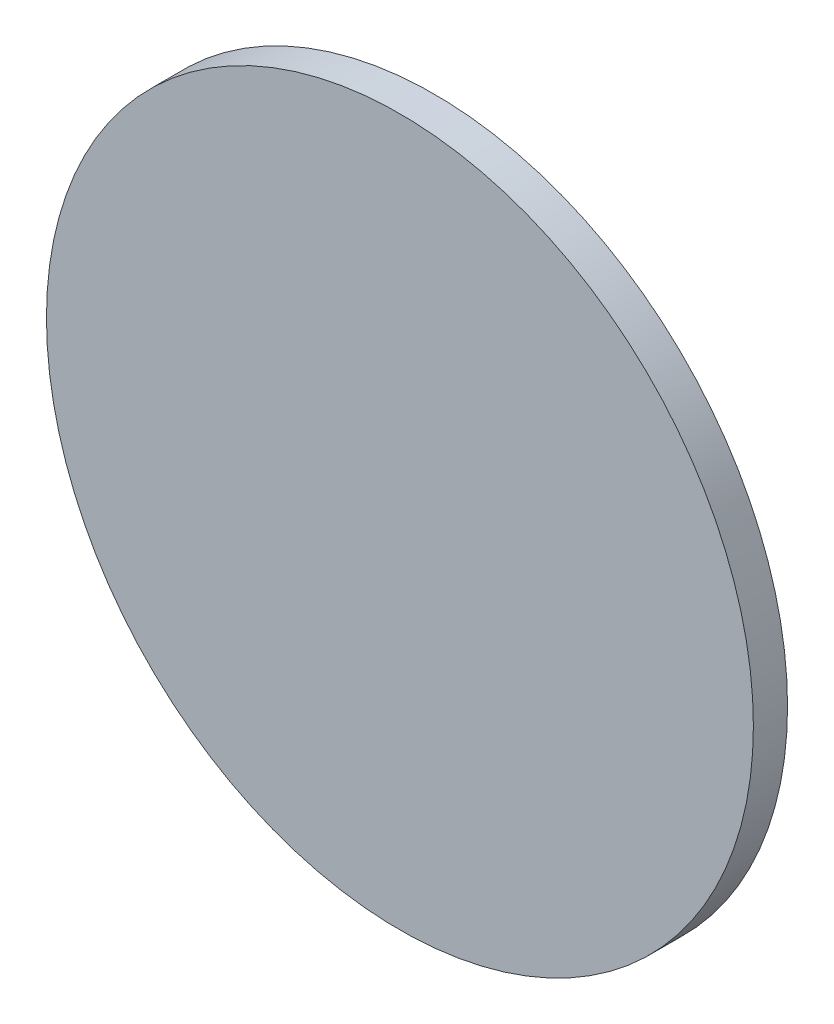
SolidWorks part; units mm, degrees
material "Bismuth"
ref_plane "Front" through (0, 0, 0) normal (0, 0, 1) x (1, 0, 0)
ref_plane "Top" through (0, 0, 0) normal (0, 1, 0) x (1, 0, 0)
ref_plane "Right" through (0, 0, 0) normal (1, 0, 0) x (0, 0, -1)
sketch "Sketch1" plane through (0, 0, 0) normal (0, 0, 1) x (1, 0, 0)
  circle A0 centre (0, 0) radius 133.5
extrude "Boss-Extrude1" add sketch "Sketch1" along normal blind 12.9
